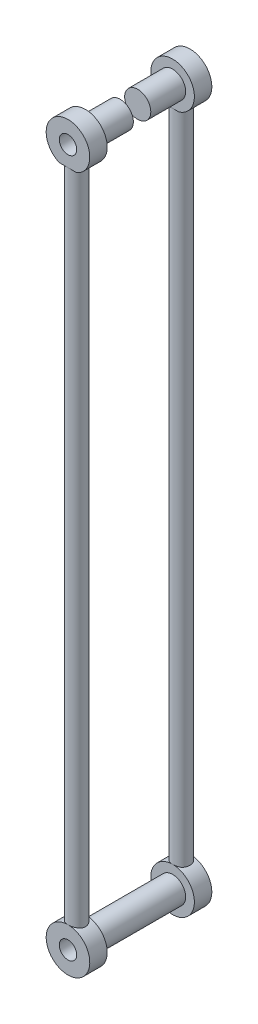
SolidWorks part; units mm, degrees
ref_plane "Front Plane" through (0, 0, 0) normal (0, 0, 1) x (1, 0, 0)
ref_plane "Top Plane" through (0, 0, 0) normal (0, 1, 0) x (1, 0, 0)
ref_plane "Right Plane" through (0, 0, 0) normal (1, 0, 0) x (0, 0, -1)
sketch "Sketch1" plane through (0, 0, 0) normal (0, 0, 1) x (1, 0, 0)
  line L0 (0, 0) -> (0, -400)
  circle A0 centre (0, 0) radius 5
  circle A1 centre (0, 0) radius 12.5
extrude "Boss-Extrude1" add sketch "Sketch1" along normal blind 10
sketch "Sketch2" plane through (0, 0, 10) normal (0, 0, 1) x (1, 0, 0)
  line L0 (0, 0) -> (0, -12)
  line L1 (0, -12) -> (9.1081, -12)
  line L2 (9.1081, -12) -> (-7.4949, -12)
  line L3 (-7.4949, -12) -> (-7.4949, -13.6285)
  line L4 (-7.4949, -13.6285) -> (9.5114, -13.6285)
  line L5 (9.5114, -13.6285) -> (9.1081, -12)
  circle M5 centre (0, 0) radius 12.5
extrude "Cut-Extrude2" cut sketch "Sketch2" against normal through all contours L4 L5 L1 L2 L3 M5 | L1 L2 M5
sketch "Sketch3" plane through (0, -12, 0) normal (0, -1, 0) x (-1, 0, 0)
  circle A0 centre (0, -5) radius 5
extrude "Boss-Extrude2" add sketch "Sketch3" along normal blind 188
mirror "Mirror2" about plane through (0, -200, 5) normal (0, -1, 0) of "Boss-Extrude2", "Boss-Extrude1"
sketch "Sketch5" plane through (0, 0, 0) normal (0, 0, 1) x (1, 0, 0)
  line L0 (0, 0) -> (0, -388)
  line L1 (-5, -388) -> (5, -388) construction
  line L2 (0, -388) -> (0, -400)
  circle A0 centre (0, -400) radius 5
  circle A1 centre (0, -400) radius 12.5
  dimension "D1" = 25
extrude "Boss-Extrude4" add sketch "Sketch5" along normal blind 10
sketch "Sketch7" plane through (0, 0, 10) normal (0, 0, 1) x (1, 0, 0)
  circle A0 centre (0, 0) radius 7.5
  circle A1 centre (0, -400) radius 7.5
  dimension "D1" = 15
  dimension "D2" = 15
extrude "Boss-Extrude5" add sketch "Sketch7" along normal blind 50 separate body
sketch "Sketch8" plane through (0, 0, 60) normal (0, 0, 1) x (1, 0, 0)
  circle A0 centre (0, 0) radius 12.5
  circle A1 centre (0, 0) radius 5
  circle A2 centre (0, -400) radius 5
  circle A3 centre (0, -400) radius 12.5
extrude "Boss-Extrude6" add sketch "Sketch8" along normal blind 10 separate body
sketch "Sketch9" plane through (0, 0, 70) normal (0, 0, 1) x (1, 0, 0)
  line L0 (0, 0) -> (0, -12.5)
  line L1 (-5, -12) -> (-5, -11.4564)
  line L2 (-5, -11.4564) -> (5, -11.4564)
  line L3 (5, -11.4564) -> (5, -13.442)
  line L4 (5, -13.442) -> (-5, -12)
  circle A1 centre (0, 0) radius 12.5 construction
  circle M1 centre (0, 0) radius 12.5
extrude "Cut-Extrude3" cut sketch "Sketch9" against normal blind 20 contours L2 L0 M1 | L2 L0 M1 | L4 L3 L1 M1
sketch "Sketch10" plane through (0, -11.4564, 0) normal (0, -1, 0) x (-1, 0, 0)
  circle A0 centre (0, -65) radius 5
extrude "Boss-Extrude7" add sketch "Sketch10" along normal blind 380
sketch "Sketch11" plane through (0, 0, 0) normal (1, 0, 0) x (0, 0, -1)
  line L0 (-30, 7.5) -> (-40, 7.5)
  line L1 (-40, 7.5) -> (-35, 7.5)
  line L2 (-35, 7.5) -> (-40, 7.5)
  line L3 (-40, 7.5) -> (-30, 7.5)
  line L4 (-30, 7.5) -> (-30, -18.877)
  line L6 (-40, -18.877) -> (-40, 7.5)
  line L7 (-30, -18.877) -> (-40, -18.877)
extrude "Cut-Extrude5" cut sketch "Sketch11" against normal through all both and the other way through all contours L7 L4 L0 L6
